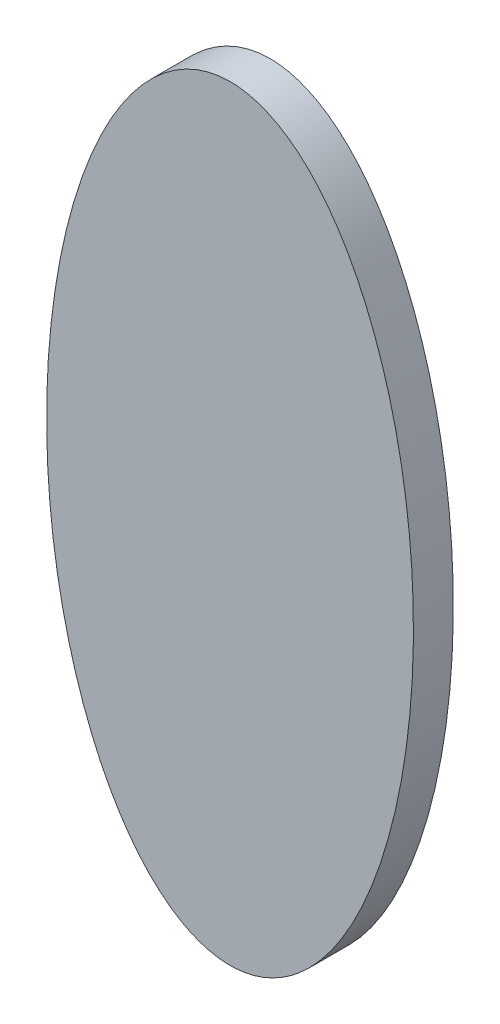
SolidWorks part; units mm, degrees
ref_plane "Спереди" through (0, 0, 0) normal (0, 0, 1) x (1, 0, 0)
ref_plane "Сверху" through (0, 0, 0) normal (0, 1, 0) x (1, 0, 0)
ref_plane "Справа" through (0, 0, 0) normal (1, 0, 0) x (0, 0, -1)
sketch "Эскиз1" plane through (0, 0, 0) normal (0, 0, 1) x (1, 0, 0)
  ellipse E0 centre (0, 0) end of major axis (0, 96) minor radius 46
  dimension "D1" = 92
  dimension "D2" = 192
extrude "Бобышка-Вытянуть1" add sketch "Эскиз1" along normal blind 10
